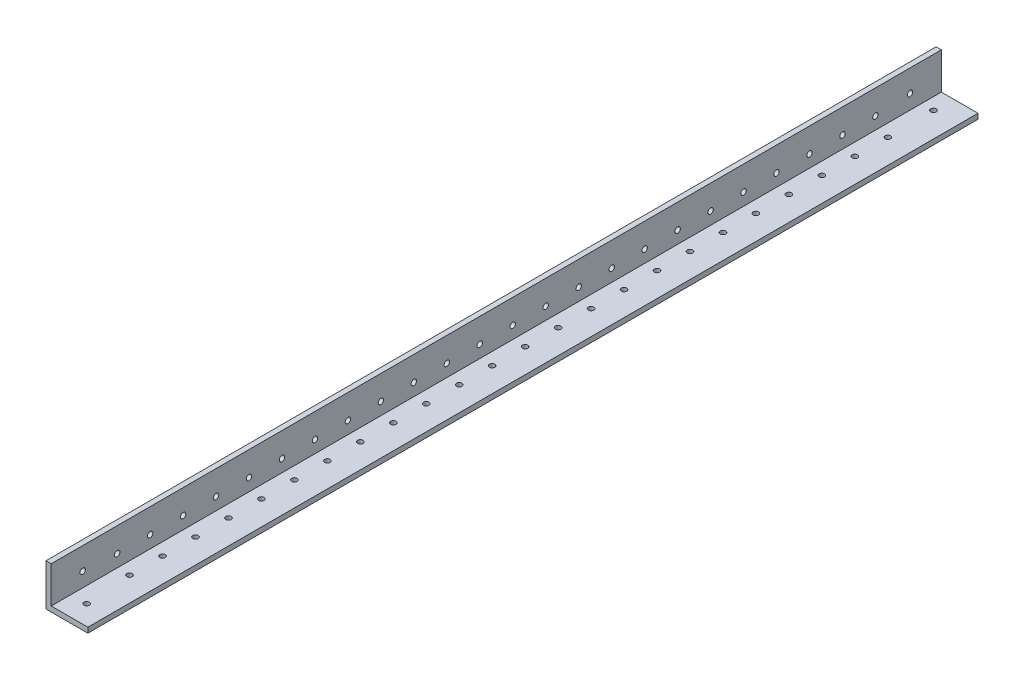
SolidWorks part; units mm, degrees
material "6061-T6 (SS)"
ref_plane "Front Plane" through (0, 0, 0) normal (0, 0, 1) x (1, 0, 0)
ref_plane "Top Plane" through (0, 0, 0) normal (0, 1, 0) x (1, 0, 0)
ref_plane "Right Plane" through (0, 0, 0) normal (1, 0, 0) x (0, 0, -1)
sketch "Sketch1" plane through (0, 0, 0) normal (0, 0, 1) x (1, 0, 0)
  line L0 (0, 25.4) -> (0, 0) construction
  line L1 (0, 0) -> (25.4, 0) construction
  line L2 (25.4, 0) -> (25.4, 3.175) construction
  line L3 (25.4, 3.175) -> (3.175, 3.175) construction
  line L4 (3.175, 3.175) -> (3.175, 25.4) construction
  line L6 (3.175, 25.4) -> (0, 25.4) construction
  arc A0 (3.175, 3.5814) -> (3.5814, 3.175) centre (3.5814, 3.5814) ccw construction
  point P4 (0, 0)
  dimension "Inside Corner Radius" = 0.4064
  dimension "Outside Height" = 25.4
  dimension "Inside Height" = 22.225
  dimension "Outside Width" = 25.4
  dimension "Inside Width" = 22.225
  dimension "Wall Thickness" = 3.175
  dimension "Shape" = 90
sketch "Sketch2" plane through (0, 0, 0) normal (1, 0, 0) x (0, 0, -1)
  line L0 (1219.2, 0) -> (-1219.2, 0) construction
  line L1 (-1219.2, 25.4) -> (-1219.2, 0) construction
  line L2 (1219.2, 25.4) -> (1219.2, 0) construction
  point P0 (-1189.99, 0)
  point P4 (0, 0)
  point P6 (1189.99, 0)
  dimension "D1" = 29.21
  dimension "D2" = 29.21
  dimension "D3" = 25.4
  dimension "Length" = 2438.4
sketch "Sketch3" plane through (0, 0, 0) normal (0, 0, 1) x (1, 0, 0)
  line L0 (3.175, 25.4) -> (0, 25.4)
  line L1 (0, 25.4) -> (0, 0)
  line L2 (0, 0) -> (25.4, 0)
  line L3 (25.4, 0) -> (25.4, 3.175)
  line L4 (25.4, 3.175) -> (3.175, 3.175)
  line L5 (3.175, 3.175) -> (3.175, 25.4)
extrude "Boss-Extrude1" add sketch "Sketch3" along normal mid plane 2438.4
fillet "Fillet1" radius 0.4064 1 edges at (3.175, 3.175, 0)
sketch "Sketch4" plane through (0, 0, 0) normal (-1, 0, 0) x (0, 0, 1)
  line L0 (1219.2, 25.4) -> (1219.2, 0) construction
  line L1 (-1219.2, 25.4) -> (679.2, 25.4)
  line L2 (-1219.2, 25.4) -> (-1219.2, -77.8785)
  line L3 (-1219.2, -77.8785) -> (679.2, -77.8785)
  line L4 (679.2, 25.4) -> (679.2, -77.8785)
  dimension "D1" = 540
extrude "Cut-Extrude1" cut sketch "Sketch4" against normal blind 60
sketch "Sketch5" plane through (0, 0, 679.2) normal (0, 0, -1) x (-1, 0, 0)
  line L0 (-3.175, 3.5814) -> (-3.175, 25.4) construction
  line L1 (-3.175, 6.1219) -> (-5.652, 6.1219)
  line L2 (-3.175, 6.1219) -> (-3.175, 3.175)
  line L3 (-3.175, 3.175) -> (-5.652, 3.175)
  line L4 (-5.652, 6.1219) -> (-5.652, 3.175)
  line L5 (-25.4, 3.175) -> (-3.5814, 3.175) construction
extrude "Cut-Extrude2" cut sketch "Sketch5" against normal blind 600
sketch "Sketch8" plane through (3.175, 0, 0) normal (1, 0, 0) x (0, 0, -1)
  line L0 (-1219.2, 3.175) -> (-1219.2, 25.4) construction
  line L1 (-1219.2, 3.175) -> (-679.2, 3.175) construction
  line L2 (-679.2, 3.175) -> (-679.2, 25.4) construction
  circle A0 centre (-1179.2, 10.675) radius 1.65
  circle A1 centre (-1159.2, 10.675) radius 1.65
  circle A2 centre (-1139.2, 10.675) radius 1.65
  circle A3 centre (-1119.2, 10.675) radius 1.65
  circle A4 centre (-1099.2, 10.675) radius 1.65
  circle A5 centre (-1079.2, 10.675) radius 1.65
  circle A6 centre (-1059.2, 10.675) radius 1.65
  circle A7 centre (-1039.2, 10.675) radius 1.65
  circle A8 centre (-1019.2, 10.675) radius 1.65
  circle A9 centre (-999.2, 10.675) radius 1.65
  circle A10 centre (-979.2, 10.675) radius 1.65
  circle A11 centre (-959.2, 10.675) radius 1.65
  circle A12 centre (-939.2, 10.675) radius 1.65
  circle A13 centre (-919.2, 10.675) radius 1.65
  circle A14 centre (-899.2, 10.675) radius 1.65
  circle A15 centre (-879.2, 10.675) radius 1.65
  circle A16 centre (-859.2, 10.675) radius 1.65
  circle A17 centre (-839.2, 10.675) radius 1.65
  circle A18 centre (-819.2, 10.675) radius 1.65
  circle A19 centre (-799.2, 10.675) radius 1.65
  circle A20 centre (-779.2, 10.675) radius 1.65
  circle A21 centre (-759.2, 10.675) radius 1.65
  circle A22 centre (-739.2, 10.675) radius 1.65
  circle A23 centre (-719.2, 10.675) radius 1.65
  dimension "D1" = 40
  dimension "D2" = 3.3
  dimension "D3" = 7.5
  dimension "D5" = 40
  dimension "D4" = 24
extrude "Cut-Extrude4" cut sketch "Sketch8" against normal blind 20
sketch "Sketch9" plane through (0, 3.175, 0) normal (0, 1, 0) x (1, 0, 0)
  line L0 (25.4, -1219.2) -> (3.175, -1219.2) construction
  line L1 (3.175, -1219.2) -> (3.175, -679.2) construction
  line L2 (25.4, -679.2) -> (3.175, -679.2) construction
  circle A0 centre (10.675, -1179.2) radius 1.65
  circle A1 centre (10.675, -1159.2) radius 1.65
  circle A2 centre (10.675, -1139.2) radius 1.65
  circle A3 centre (10.675, -1119.2) radius 1.65
  circle A4 centre (10.675, -1099.2) radius 1.65
  circle A5 centre (10.675, -1079.2) radius 1.65
  circle A6 centre (10.675, -1059.2) radius 1.65
  circle A7 centre (10.675, -1039.2) radius 1.65
  circle A8 centre (10.675, -1019.2) radius 1.65
  circle A9 centre (10.675, -999.2) radius 1.65
  circle A10 centre (10.675, -979.2) radius 1.65
  circle A11 centre (10.675, -959.2) radius 1.65
  circle A12 centre (10.675, -939.2) radius 1.65
  circle A13 centre (10.675, -919.2) radius 1.65
  circle A14 centre (10.675, -899.2) radius 1.65
  circle A15 centre (10.675, -879.2) radius 1.65
  circle A16 centre (10.675, -859.2) radius 1.65
  circle A17 centre (10.675, -839.2) radius 1.65
  circle A18 centre (10.675, -819.2) radius 1.65
  circle A19 centre (10.675, -799.2) radius 1.65
  circle A20 centre (10.675, -779.2) radius 1.65
  circle A21 centre (10.675, -759.2) radius 1.65
  circle A22 centre (10.675, -739.2) radius 1.65
  circle A23 centre (10.675, -719.2) radius 1.65
  dimension "D1" = 40
  dimension "D2" = 3.3
  dimension "D3" = 7.5
  dimension "D4" = 24
  dimension "D5" = 40
extrude "Cut-Extrude5" cut sketch "Sketch9" against normal blind 20
sketch "Sketch10" plane through (3.175, 0, 0) normal (1, 0, 0) x (0, 0, -1)
  circle A0 centre (-1200.15, 11.9634) radius 1.65
  circle A1 centre (-698.25, 11.9634) radius 1.65
  dimension "D1" = 3.3
extrude "Cut-Extrude6" cut sketch "Sketch10" against normal blind 70
sketch "Sketch11" plane through (0, 3.175, 0) normal (0, 1, 0) x (1, 0, 0)
  circle A0 centre (10.3644, -691.1957) radius 1.65
  circle A1 centre (12.7, -1207.2043) radius 1.65
  dimension "D1" = 3.3
extrude "Cut-Extrude7" cut sketch "Sketch11" against normal blind 70
equation "\"D1@Boss-Extrude1\"=\"Length@Sketch2\""
equation "\"D1@Sketch2\" = \"Outside Width@Sketch1\" * 1.15"
equation "\"D2@Sketch2\"=\"D1@Sketch2\""
equation "\"D1@Fillet1\"=\"Inside Corner Radius@Sketch1\""
equation "\"D3@Sketch2\"=\"Outside Height@Sketch1\""
